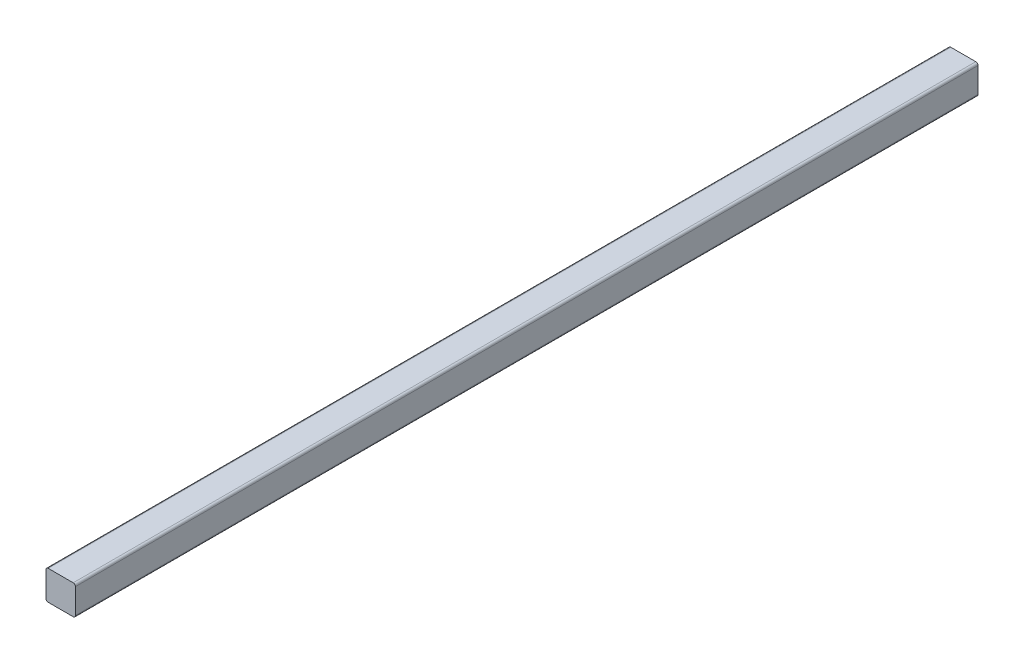
SolidWorks part; units mm, degrees
ref_plane "Plan de face" through (0, 0, 0) normal (0, 0, 1) x (1, 0, 0)
ref_plane "Plan de dessus" through (0, 0, 0) normal (0, 1, 0) x (1, 0, 0)
ref_plane "Plan de droite" through (0, 0, 0) normal (1, 0, 0) x (0, 0, -1)
sketch "Esquisse1" plane through (0, 0, 0) normal (0, 0, 1) x (1, 0, 0)
  line L0 (0, -63.3691) -> (0, 71.2902) construction
  line L1 (-75.6108, 0) -> (80.6515, 0) construction
  line L2 (-15, 12.75) -> (-15, -12.75)
  line L3 (-12.75, 15) -> (12.75, 15)
  line L4 (-12.75, -15) -> (12.75, -15)
  line L6 (15, 12.75) -> (15, -12.75)
  arc A0 (12.75, 15) -> (15, 12.75) centre (12.75, 12.75) cw
  arc A1 (-12.75, 15) -> (-15, 12.75) centre (-12.75, 12.75) ccw
  arc A2 (-12.75, -15) -> (-15, -12.75) centre (-12.75, -12.75) cw
  arc A3 (12.75, -15) -> (15, -12.75) centre (12.75, -12.75) ccw
  point P5 (-15, 0)
  point P14 (0, 15)
  point P20 (0, -15)
  point P21 (15, 0)
  dimension "D3" = 2.25
  dimension "D1" = 30
  dimension "D2" = 30
extrude "Extrusion1" add sketch "Esquisse1" along normal blind 920
